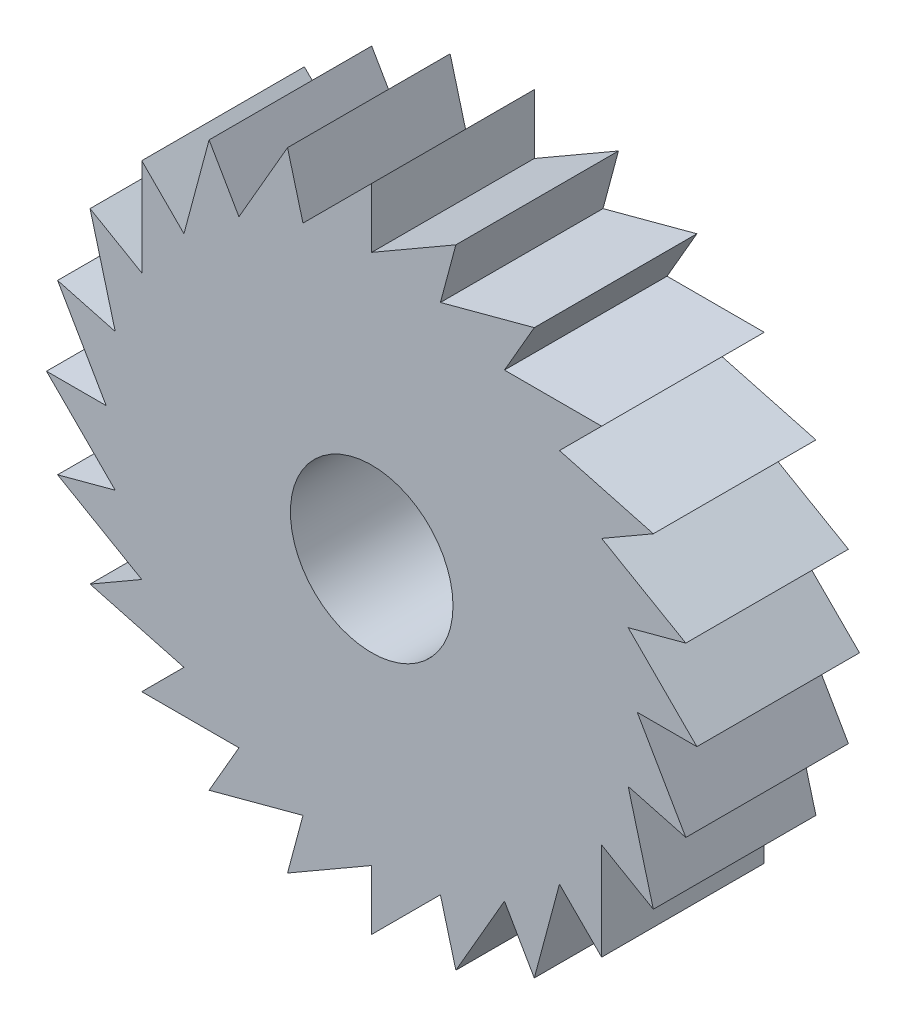
SolidWorks part; units mm, degrees
ref_plane "Front Plane" through (0, 0, 0) normal (0, 0, 1) x (1, 0, 0)
ref_plane "Top Plane" through (0, 0, 0) normal (0, 1, 0) x (1, 0, 0)
ref_plane "Right Plane" through (0, 0, 0) normal (1, 0, 0) x (0, 0, -1)
sketch "Sketch1" plane through (0, 0, 0) normal (0, 0, 1) x (1, 0, 0)
  line L0 (0, 0) -> (0, 12.7) construction
  line L1 (0, 0) -> (3.287, 12.2673) construction
  line L2 (3.287, 12.2673) -> (0, 10.3695)
  line L3 (0, 10.3695) -> (0, 12.7)
  line L4 (6.35, 10.9985) -> (2.6838, 10.0162)
  line L5 (2.6838, 10.0162) -> (3.287, 12.2673)
  line L6 (8.9803, 8.9803) -> (5.1848, 8.9803)
  line L7 (5.1848, 8.9803) -> (6.35, 10.9985)
  line L8 (10.9985, 6.35) -> (7.3323, 7.3323)
  line L9 (7.3323, 7.3323) -> (8.9803, 8.9803)
  line L10 (12.2673, 3.287) -> (8.9803, 5.1848)
  line L11 (8.9803, 5.1848) -> (10.9985, 6.35)
  line L12 (12.7, 0) -> (10.0162, 2.6838)
  line L13 (10.0162, 2.6838) -> (12.2673, 3.287)
  line L14 (12.2673, -3.287) -> (10.3695, 0)
  line L15 (10.3695, 0) -> (12.7, 0)
  line L16 (10.9985, -6.35) -> (10.0162, -2.6838)
  line L17 (10.0162, -2.6838) -> (12.2673, -3.287)
  line L18 (8.9803, -8.9803) -> (8.9803, -5.1848)
  line L19 (8.9803, -5.1848) -> (10.9985, -6.35)
  line L20 (6.35, -10.9985) -> (7.3323, -7.3323)
  line L21 (7.3323, -7.3323) -> (8.9803, -8.9803)
  line L22 (3.287, -12.2673) -> (5.1848, -8.9803)
  line L23 (5.1848, -8.9803) -> (6.35, -10.9985)
  line L24 (0, -12.7) -> (2.6838, -10.0162)
  line L25 (2.6838, -10.0162) -> (3.287, -12.2673)
  line L26 (-3.287, -12.2673) -> (0, -10.3695)
  line L27 (0, -10.3695) -> (0, -12.7)
  line L28 (-6.35, -10.9985) -> (-2.6838, -10.0162)
  line L29 (-2.6838, -10.0162) -> (-3.287, -12.2673)
  line L30 (-8.9803, -8.9803) -> (-5.1848, -8.9803)
  line L31 (-5.1848, -8.9803) -> (-6.35, -10.9985)
  line L32 (-10.9985, -6.35) -> (-7.3323, -7.3323)
  line L33 (-7.3323, -7.3323) -> (-8.9803, -8.9803)
  line L34 (-12.2673, -3.287) -> (-8.9803, -5.1848)
  line L35 (-8.9803, -5.1848) -> (-10.9985, -6.35)
  line L36 (-12.7, 0) -> (-10.0162, -2.6838)
  line L37 (-10.0162, -2.6838) -> (-12.2673, -3.287)
  line L38 (-12.2673, 3.287) -> (-10.3695, 0)
  line L39 (-10.3695, 0) -> (-12.7, 0)
  line L40 (-10.9985, 6.35) -> (-10.0162, 2.6838)
  line L41 (-10.0162, 2.6838) -> (-12.2673, 3.287)
  line L42 (-8.9803, 8.9803) -> (-8.9803, 5.1848)
  line L43 (-8.9803, 5.1848) -> (-10.9985, 6.35)
  line L44 (-6.35, 10.9985) -> (-7.3323, 7.3323)
  line L45 (-7.3323, 7.3323) -> (-8.9803, 8.9803)
  line L46 (-3.287, 12.2673) -> (-5.1848, 8.9803)
  line L47 (-5.1848, 8.9803) -> (-6.35, 10.9985)
  line L48 (0, 12.7) -> (-2.6838, 10.0162)
  line L49 (-2.6838, 10.0162) -> (-3.287, 12.2673)
  circle A0 centre (0, 0) radius 12.7 construction
  circle A1 centre (0, 0) radius 3.175
  point P78 (0, 0)
  dimension "D1" = 25.4
  dimension "D5" = 6.35
  dimension "D2" = 15
  dimension "D3" = 60
  dimension "D4" = 24
extrude "Boss-Extrude1" add sketch "Sketch1" along normal blind 6.35 contours L48 L49 L46 L47 L44 L45 L42 L43 L40 L41 L38 L39 L36 L37 L34 L35 L32 L33 L30 L31 L28 L29 L26 L27 L24 L25 L22 L23 L20 L21 L18 L19 L16 L17 L14 L15 L12 L13 L10 L11 L8 L9 L6 L7 L4 L5 L2 L3 A1
